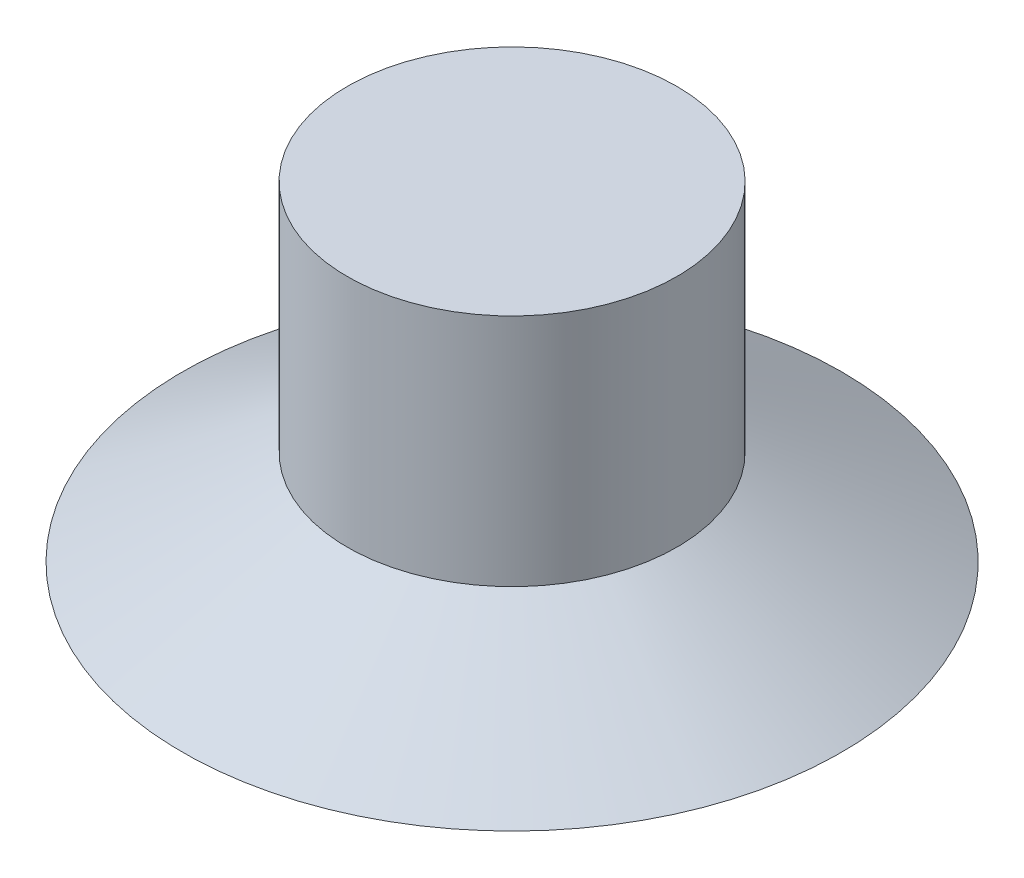
SolidWorks part; units mm, degrees
ref_plane "Plan de face" through (0, 0, 0) normal (0, 0, 1) x (1, 0, 0)
ref_plane "Plan de dessus" through (0, 0, 0) normal (0, 1, 0) x (1, 0, 0)
ref_plane "Plan de droite" through (0, 0, 0) normal (1, 0, 0) x (0, 0, -1)
sketch "Esquisse1" plane through (0, 0, 0) normal (0, 0, 1) x (1, 0, 0)
  line L0 (0, 0) -> (0, 51.0922) construction
  line L1 (0, 0) -> (8, 0)
  line L2 (8, 0) -> (4, 2.3094)
  line L3 (4, 2.3094) -> (4, 8)
  line L4 (4, 8) -> (0, 8)
  line L5 (0, 8) -> (0, 0)
  dimension "D1" = 8
  dimension "D2" = 4
  dimension "D3" = 30
  dimension "D4" = 8
revolve "Révolution1" add sketch "Esquisse1" angle 360 about L0
sketch "Esquisse2" plane through (0, 0, 0) normal (0, -1, 0) x (1, 0, 0)
  line L0 (-3.4641, 0) -> (-1.7321, 3)
  line L1 (-1.7321, 3) -> (1.7321, 3)
  line L2 (1.7321, 3) -> (3.4641, 0)
  line L3 (3.4641, 0) -> (1.7321, -3)
  line L4 (1.7321, -3) -> (-1.7321, -3)
  line L5 (-1.7321, -3) -> (-3.4641, 0)
  line L6 (-1.7321, 3) -> (1.7321, -3) construction
  line L7 (1.7321, 3) -> (-1.7321, -3) construction
  point P6 (0, 0)
  dimension "D1" = 120
  dimension "D2" = 120
  dimension "D3" = 6
extrude "Enlèv. mat.-Extru.1" cut sketch "Esquisse2" against normal blind 3
